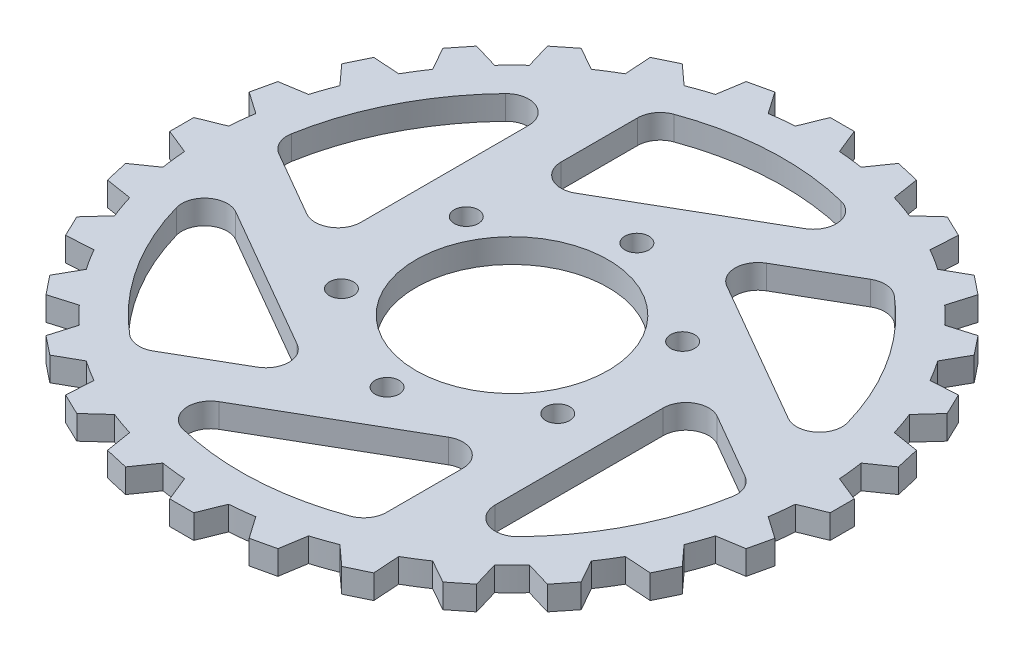
SolidWorks part; units mm, degrees
ref_plane "Front Plane" through (0, 0, 0) normal (0, 0, 1) x (1, 0, 0)
ref_plane "Top Plane" through (0, 0, 0) normal (0, 1, 0) x (1, 0, 0)
ref_plane "Right Plane" through (0, 0, 0) normal (1, 0, 0) x (0, 0, -1)
sketch "Sketch1" plane through (0, 0, 0) normal (0, 1, 0) x (1, 0, 0)
  line L0 (0, 122.3506) -> (0, -152.6083) construction
  line L1 (-171.9701, 0) -> (161.7432, 0) construction
  line L2 (-45, 97.2214) -> (-45, 65.4545)
  line L3 (-30.75, 57.2272) -> (29.8119, 92.1926)
  line L4 (-45, 65.4545) -> (-45, 49) construction
  line L5 (-30.75, 57.2272) -> (-45, 49)
  line L6 (61.6962, 87.5818) -> (34.1852, 71.6984)
  line L7 (34.1852, 55.2439) -> (94.7471, 20.2785)
  line L8 (106.6962, -9.6396) -> (79.1852, 6.2439)
  line L9 (64.9352, -1.9833) -> (64.9352, -71.9141)
  line L10 (45, -97.2214) -> (45, -65.4545)
  line L11 (30.75, -57.2272) -> (-29.8119, -92.1926)
  line L12 (-61.6962, -87.5818) -> (-34.1852, -71.6984)
  line L13 (-34.1852, -55.2439) -> (-94.7471, -20.2785)
  line L14 (-106.6962, 9.6396) -> (-79.1852, -6.2439)
  line L15 (-64.9352, 1.9833) -> (-64.9352, 71.9141)
  line L16 (-5, -137.5) -> (5, -137.5)
  line L17 (-5, -137.5) -> (-9.1738, -127.1695)
  line L18 (5, -137.5) -> (9.1738, -127.1695)
  line L19 (-35.4713, -132.94) -> (-37.2417, -121.9398)
  line L20 (-35.4713, -132.94) -> (-25.722, -135.1652)
  line L21 (-25.722, -135.1652) -> (-19.3541, -126.0225)
  line L22 (-64.1639, -121.7138) -> (-63.4421, -110.5954)
  line L23 (-64.1639, -121.7138) -> (-55.1542, -126.0526)
  line L24 (-55.1542, -126.0526) -> (-46.9115, -118.5561)
  line L25 (-89.639, -104.3844) -> (-86.4613, -93.7054)
  line L26 (-89.639, -104.3844) -> (-81.8207, -110.6193)
  line L27 (-81.8207, -110.6193) -> (-72.1166, -105.1449)
  line L28 (-110.6193, -81.8207) -> (-105.1449, -72.1166)
  line L29 (-110.6193, -81.8207) -> (-104.3844, -89.639)
  line L30 (-104.3844, -89.639) -> (-93.7054, -86.4613)
  line L31 (-126.0526, -55.1542) -> (-118.5561, -46.9115)
  line L32 (-126.0526, -55.1542) -> (-121.7138, -64.1639)
  line L33 (-121.7138, -64.1639) -> (-110.5954, -63.4421)
  line L34 (-135.1652, -25.722) -> (-126.0225, -19.3541)
  line L35 (-135.1652, -25.722) -> (-132.94, -35.4713)
  line L36 (-132.94, -35.4713) -> (-121.9398, -37.2417)
  line L37 (-137.5, 5) -> (-127.1695, 9.1738)
  line L38 (-137.5, 5) -> (-137.5, -5)
  line L39 (-137.5, -5) -> (-127.1695, -9.1738)
  line L40 (-132.94, 35.4713) -> (-121.9398, 37.2417)
  line L41 (-132.94, 35.4713) -> (-135.1652, 25.722)
  line L42 (-135.1652, 25.722) -> (-126.0225, 19.3541)
  line L43 (-121.7138, 64.1639) -> (-110.5954, 63.4421)
  line L44 (-121.7138, 64.1639) -> (-126.0526, 55.1542)
  line L45 (-126.0526, 55.1542) -> (-118.5561, 46.9115)
  line L46 (-104.3844, 89.639) -> (-93.7054, 86.4613)
  line L47 (-104.3844, 89.639) -> (-110.6193, 81.8207)
  line L48 (-110.6193, 81.8207) -> (-105.1449, 72.1166)
  line L49 (-81.8207, 110.6193) -> (-72.1166, 105.1449)
  line L50 (-81.8207, 110.6193) -> (-89.639, 104.3844)
  line L51 (-89.639, 104.3844) -> (-86.4613, 93.7054)
  line L52 (-55.1542, 126.0526) -> (-46.9115, 118.5561)
  line L53 (-55.1542, 126.0526) -> (-64.1639, 121.7138)
  line L54 (-64.1639, 121.7138) -> (-63.4421, 110.5954)
  line L55 (-25.722, 135.1652) -> (-19.3541, 126.0225)
  line L56 (-25.722, 135.1652) -> (-35.4713, 132.94)
  line L57 (-35.4713, 132.94) -> (-37.2417, 121.9398)
  line L58 (5, 137.5) -> (9.1738, 127.1695)
  line L59 (5, 137.5) -> (-5, 137.5)
  line L60 (-5, 137.5) -> (-9.1738, 127.1695)
  line L61 (35.4713, 132.94) -> (37.2417, 121.9398)
  line L62 (35.4713, 132.94) -> (25.722, 135.1652)
  line L63 (25.722, 135.1652) -> (19.3541, 126.0225)
  line L64 (64.1639, 121.7138) -> (63.4421, 110.5954)
  line L65 (64.1639, 121.7138) -> (55.1542, 126.0526)
  line L66 (55.1542, 126.0526) -> (46.9115, 118.5561)
  line L67 (89.639, 104.3844) -> (86.4613, 93.7054)
  line L68 (89.639, 104.3844) -> (81.8207, 110.6193)
  line L69 (81.8207, 110.6193) -> (72.1166, 105.1449)
  line L70 (110.6193, 81.8207) -> (105.1449, 72.1166)
  line L71 (110.6193, 81.8207) -> (104.3844, 89.639)
  line L72 (104.3844, 89.639) -> (93.7054, 86.4613)
  line L73 (126.0526, 55.1542) -> (118.5561, 46.9115)
  line L74 (126.0526, 55.1542) -> (121.7138, 64.1639)
  line L75 (121.7138, 64.1639) -> (110.5954, 63.4421)
  line L76 (135.1652, 25.722) -> (126.0225, 19.3541)
  line L77 (135.1652, 25.722) -> (132.94, 35.4713)
  line L78 (132.94, 35.4713) -> (121.9398, 37.2417)
  line L79 (137.5, -5) -> (127.1695, -9.1738)
  line L80 (137.5, -5) -> (137.5, 5)
  line L81 (137.5, 5) -> (127.1695, 9.1738)
  line L82 (132.94, -35.4713) -> (121.9398, -37.2417)
  line L83 (132.94, -35.4713) -> (135.1652, -25.722)
  line L84 (135.1652, -25.722) -> (126.0225, -19.3541)
  line L85 (121.7138, -64.1639) -> (110.5954, -63.4421)
  line L86 (121.7138, -64.1639) -> (126.0526, -55.1542)
  line L87 (126.0526, -55.1542) -> (118.5561, -46.9115)
  line L88 (104.3844, -89.639) -> (93.7054, -86.4613)
  line L89 (104.3844, -89.639) -> (110.6193, -81.8207)
  line L90 (110.6193, -81.8207) -> (105.1449, -72.1166)
  line L91 (81.8207, -110.6193) -> (72.1166, -105.1449)
  line L92 (81.8207, -110.6193) -> (89.639, -104.3844)
  line L93 (89.639, -104.3844) -> (86.4613, -93.7054)
  line L94 (55.1542, -126.0526) -> (46.9115, -118.5561)
  line L95 (55.1542, -126.0526) -> (64.1639, -121.7138)
  line L96 (64.1639, -121.7138) -> (63.4421, -110.5954)
  line L97 (25.722, -135.1652) -> (19.3541, -126.0225)
  line L98 (25.722, -135.1652) -> (35.4713, -132.94)
  line L99 (35.4713, -132.94) -> (37.2417, -121.9398)
  circle A0 centre (0, 0) radius 40
  circle A1 centre (0, 0) radius 52 construction
  circle A2 centre (0, 52) radius 5
  circle A3 centre (45.0333, 26) radius 5
  circle A4 centre (45.0333, -26) radius 5
  circle A5 centre (0, -52) radius 5
  circle A6 centre (-45.0333, -26) radius 5
  circle A7 centre (-45.0333, 26) radius 5
  arc A8 (-45, 65.4545) -> (-30.75, 57.2272) centre (-35.5, 65.4545) ccw
  arc A9 (-45, 97.2214) -> (-38.7585, 106.1451) centre (-35.5, 97.2214) cw
  arc A10 (-38.7585, 106.1451) -> (27.3622, 109.6372) centre (0, 0) cw
  arc A11 (27.3622, 109.6372) -> (29.8119, 92.1926) centre (25.0619, 100.4199) cw
  arc A12 (34.1852, 71.6984) -> (34.1852, 55.2439) centre (38.9352, 63.4711) ccw
  arc A13 (61.6962, 87.5818) -> (72.5451, 86.6384) centre (66.4462, 79.3546) cw
  arc A14 (72.5451, 86.6384) -> (108.6297, 31.1222) centre (0, 0) cw
  arc A15 (108.6297, 31.1222) -> (94.7471, 20.2785) centre (99.4971, 28.5057) cw
  arc A16 (79.1852, 6.2439) -> (64.9352, -1.9833) centre (74.4352, -1.9833) ccw
  arc A17 (106.6962, -9.6396) -> (111.3036, -19.5067) centre (101.9462, -17.8668) cw
  arc A18 (111.3036, -19.5067) -> (81.2675, -78.515) centre (0, 0) cw
  arc A19 (81.2675, -78.515) -> (64.9352, -71.9141) centre (74.4352, -71.9141) cw
  arc A20 (45, -65.4545) -> (30.75, -57.2272) centre (35.5, -65.4545) ccw
  arc A21 (45, -97.2214) -> (38.7585, -106.1451) centre (35.5, -97.2214) cw
  arc A22 (38.7585, -106.1451) -> (-27.3622, -109.6372) centre (0, 0) cw
  arc A23 (-27.3622, -109.6372) -> (-29.8119, -92.1926) centre (-25.0619, -100.4199) cw
  arc A24 (-34.1852, -71.6984) -> (-34.1852, -55.2439) centre (-38.9352, -63.4711) ccw
  arc A25 (-61.6962, -87.5818) -> (-72.5451, -86.6384) centre (-66.4462, -79.3546) cw
  arc A26 (-72.5451, -86.6384) -> (-108.6297, -31.1222) centre (0, 0) cw
  arc A27 (-108.6297, -31.1222) -> (-94.7471, -20.2785) centre (-99.4971, -28.5057) cw
  arc A28 (-79.1852, -6.2439) -> (-64.9352, 1.9833) centre (-74.4352, 1.9833) ccw
  arc A29 (-106.6962, 9.6396) -> (-111.3036, 19.5067) centre (-101.9462, 17.8668) cw
  arc A30 (-111.3036, 19.5067) -> (-81.2675, 78.515) centre (0, 0) cw
  arc A31 (-81.2675, 78.515) -> (-64.9352, 71.9141) centre (-74.4352, 71.9141) cw
  arc A32 (9.1738, -127.1695) -> (19.3541, -126.0225) centre (0, 0) ccw
  arc A33 (37.2417, -121.9398) -> (46.9115, -118.5561) centre (0, 0) ccw
  arc A34 (63.4421, -110.5954) -> (72.1166, -105.1449) centre (0, 0) ccw
  arc A35 (86.4613, -93.7054) -> (93.7054, -86.4613) centre (0, 0) ccw
  arc A36 (105.1449, -72.1166) -> (110.5954, -63.4421) centre (0, 0) ccw
  arc A37 (118.5561, -46.9115) -> (121.9398, -37.2417) centre (0, 0) ccw
  arc A38 (126.0225, -19.3541) -> (127.1695, -9.1738) centre (0, 0) ccw
  arc A39 (127.1695, 9.1738) -> (126.0225, 19.3541) centre (0, 0) ccw
  arc A40 (121.9398, 37.2417) -> (118.5561, 46.9115) centre (0, 0) ccw
  arc A41 (110.5954, 63.4421) -> (105.1449, 72.1166) centre (0, 0) ccw
  arc A42 (93.7054, 86.4613) -> (86.4613, 93.7054) centre (0, 0) ccw
  arc A43 (72.1166, 105.1449) -> (63.4421, 110.5954) centre (0, 0) ccw
  arc A44 (46.9115, 118.5561) -> (37.2417, 121.9398) centre (0, 0) ccw
  arc A45 (19.3541, 126.0225) -> (9.1738, 127.1695) centre (0, 0) ccw
  arc A46 (-9.1738, 127.1695) -> (-19.3541, 126.0225) centre (0, 0) ccw
  arc A47 (-37.2417, 121.9398) -> (-46.9115, 118.5561) centre (0, 0) ccw
  arc A48 (-63.4421, 110.5954) -> (-72.1166, 105.1449) centre (0, 0) ccw
  arc A49 (-86.4613, 93.7054) -> (-93.7054, 86.4613) centre (0, 0) ccw
  arc A50 (-105.1449, 72.1166) -> (-110.5954, 63.4421) centre (0, 0) ccw
  arc A51 (-118.5561, 46.9115) -> (-121.9398, 37.2417) centre (0, 0) ccw
  arc A52 (-126.0225, 19.3541) -> (-127.1695, 9.1738) centre (0, 0) ccw
  arc A53 (-127.1695, -9.1738) -> (-126.0225, -19.3541) centre (0, 0) ccw
  arc A54 (-121.9398, -37.2417) -> (-118.5561, -46.9115) centre (0, 0) ccw
  arc A55 (-110.5954, -63.4421) -> (-105.1449, -72.1166) centre (0, 0) ccw
  arc A56 (-93.7054, -86.4613) -> (-86.4613, -93.7054) centre (0, 0) ccw
  arc A57 (-72.1166, -105.1449) -> (-63.4421, -110.5954) centre (0, 0) ccw
  arc A58 (-46.9115, -118.5561) -> (-37.2417, -121.9398) centre (0, 0) ccw
  arc A59 (-19.3541, -126.0225) -> (-9.1738, -127.1695) centre (0, 0) ccw
  point P22 (0, 0)
  point P79 (0, 0)
  point P84 (0, -137.5)
  point P193 (0, 0)
  dimension "D1" = 80
  dimension "D2" = 104
  dimension "D3" = 10
  dimension "D8" = 9.5
  dimension "D9" = 9.5
  dimension "D10" = 113
  dimension "D11" = 9.5
  dimension "D13" = 255
  dimension "D5" = 45
  dimension "D6" = 30
  dimension "D7" = 49
  dimension "D14" = 10
  dimension "D15" = 10
  dimension "D16" = 44
  dimension "D17" = 22
  dimension "D4" = 6
  dimension "D12" = 6
  dimension "D18" = 28
extrude "Boss-Extrude1" add sketch "Sketch1" along normal blind 10 contours L21 A59 L17 L16 L18 A32 L97 L98 L99 A33 L94 L95 L96 A34 L91 L92 L93 A35 L88 L89 L90 A36 L85 L86 L87 A37 L82 L83 L84 A38 L79 L80 L81 A39 L76 L77 L78 A40 L73 L74 L75 A41 L70 L71 L72 A42 L67 L68 L69 A43 L64
